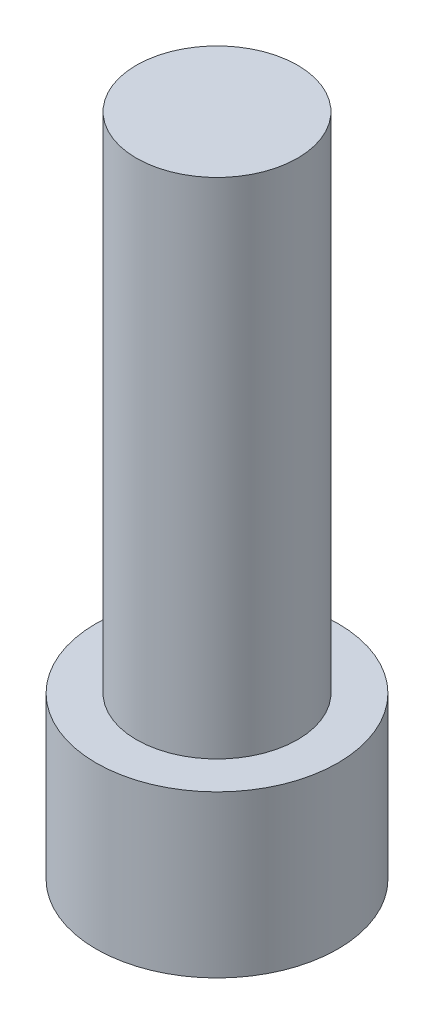
SolidWorks part; units mm, degrees
ref_plane "Front Plane" through (0, 0, 0) normal (0, 0, 1) x (1, 0, 0)
ref_plane "Top Plane" through (0, 0, 0) normal (0, 1, 0) x (1, 0, 0)
ref_plane "Right Plane" through (0, 0, 0) normal (1, 0, 0) x (0, 0, -1)
sketch "Sketch1" plane through (0, 0, 0) normal (0, 1, 0) x (1, 0, 0)
  circle A0 centre (0, 0) radius 4
  dimension "D1" = 8
extrude "Boss-Extrude1" add sketch "Sketch1" along normal blind 25
sketch "Sketch2" plane through (0, 0, 0) normal (0, -1, 0) x (1, 0, 0)
  circle A0 centre (0, 0) radius 6
  circle A1 centre (0, 0) radius 4
  circle A2 centre (0, 0) radius 4
  circle M3 centre (0, 0) radius 4
  dimension "D1" = 0
  dimension "D2" = 2
extrude "Boss-Extrude2" add sketch "Sketch2" along normal blind 2 contours A0 M3 | M3 | A2
sketch "Sketch3" plane through (0, -2, 0) normal (0, -1, 0) x (1, 0, 0)
  line L1 (4.6188, 0) -> (2.3094, 4)
  line L2 (2.3094, 4) -> (-2.3094, 4)
  line L3 (-2.3094, 4) -> (-4.6188, 0)
  line L4 (-4.6188, 0) -> (-2.3094, -4)
  line L5 (-2.3094, -4) -> (2.3094, -4)
  line L6 (2.3094, -4) -> (4.6188, 0)
  circle A0 centre (0, 0) radius 4 construction
  circle A1 centre (0, 0) radius 6
  circle A2 centre (0, 0) radius 6
  point P0 (0, 0)
  dimension "D2" = 8
  dimension "D1" = 0
extrude "Boss-Extrude3" add sketch "Sketch3" along normal blind 6
